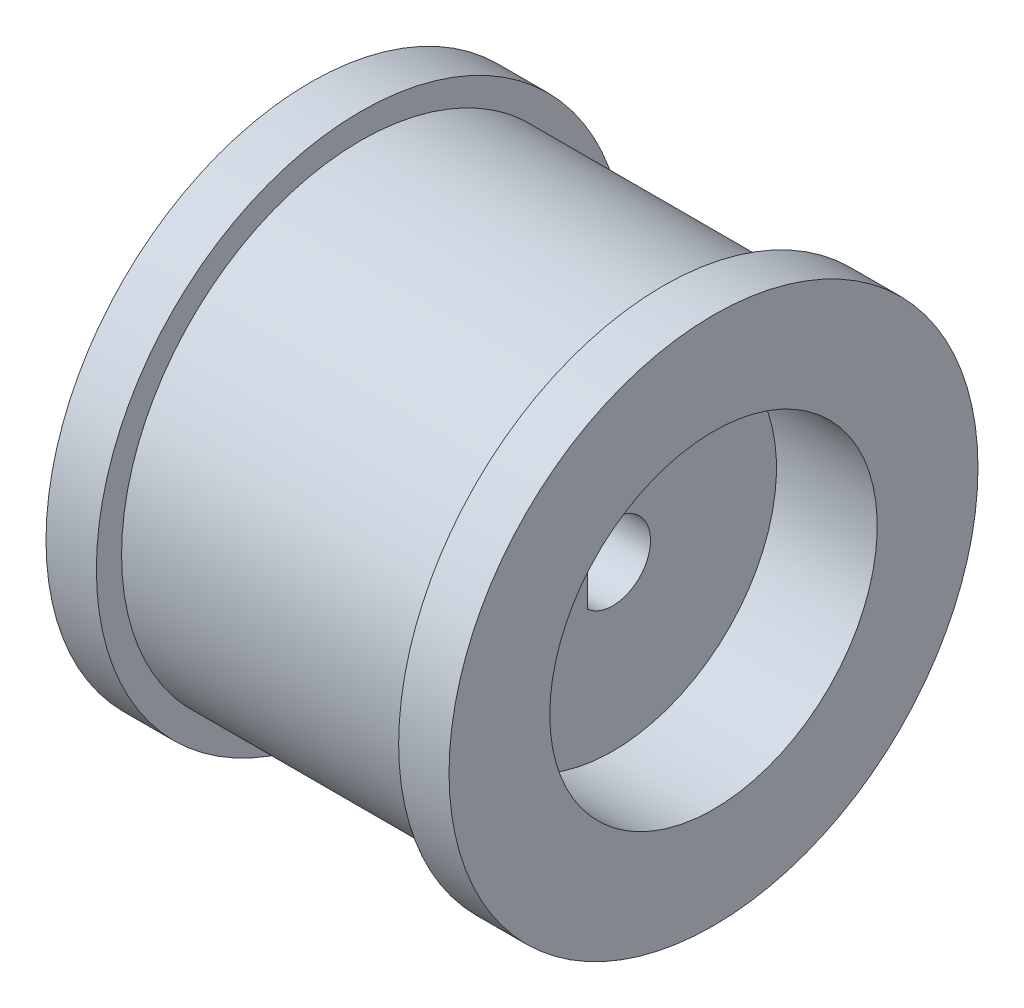
SolidWorks part; units mm, degrees
material "ABS"
ref_plane "Front Plane" through (0, 0, 0) normal (0, 0, 1) x (1, 0, 0)
ref_plane "Top Plane" through (0, 0, 0) normal (0, 1, 0) x (1, 0, 0)
ref_plane "Right Plane" through (0, 0, 0) normal (1, 0, 0) x (0, 0, -1)
sketch "Sketch1" plane through (0, 0, 0) normal (0, 0, 1) x (1, 0, 0)
  line L0 (-167.0018, 0) -> (167.0018, 0) construction
  line L1 (0, -100.3853) -> (0, 100.3853) construction
  line L2 (6, 9.5) -> (-6, 9.5)
  line L3 (-6, 9.5) -> (-6, 10.5)
  line L4 (-6, 10.5) -> (-8, 10.5)
  line L5 (-8, 10.5) -> (-8, 6.5)
  line L6 (-8, 6.5) -> (-4, 6.5)
  line L7 (-4, 6.5) -> (-4, 0)
  line L8 (-4, 0) -> (4, 0)
  line L9 (4, 6.5) -> (4, 0)
  line L10 (8, 6.5) -> (4, 6.5)
  line L11 (8, 10.5) -> (8, 6.5)
  line L12 (6, 10.5) -> (8, 10.5)
  line L13 (6, 9.5) -> (6, 10.5)
  point P4 (0, 0)
  point P7 (0, 0)
  point P16 (0, 0)
  point P21 (0, 9.5)
  dimension "D1" = 9.5
  dimension "D2" = 1
  dimension "D3" = 2
  dimension "D4" = 4
  dimension "D5" = 6
  dimension "D6" = 4
revolve "Revolve1" add sketch "Sketch1" angle 360 about L0
sketch "Sketch2" plane through (4, 0, 0) normal (1, 0, 0) x (0, 0, -1)
  line L0 (-1, 1.118) -> (-1, -1.118)
  arc A0 (-1, -1.118) -> (-1, 1.118) centre (0, 0) ccw
  dimension "D2" = 3
  dimension "D1" = 1
extrude "Cut-Extrude1" cut sketch "Sketch2" against normal blind 10
